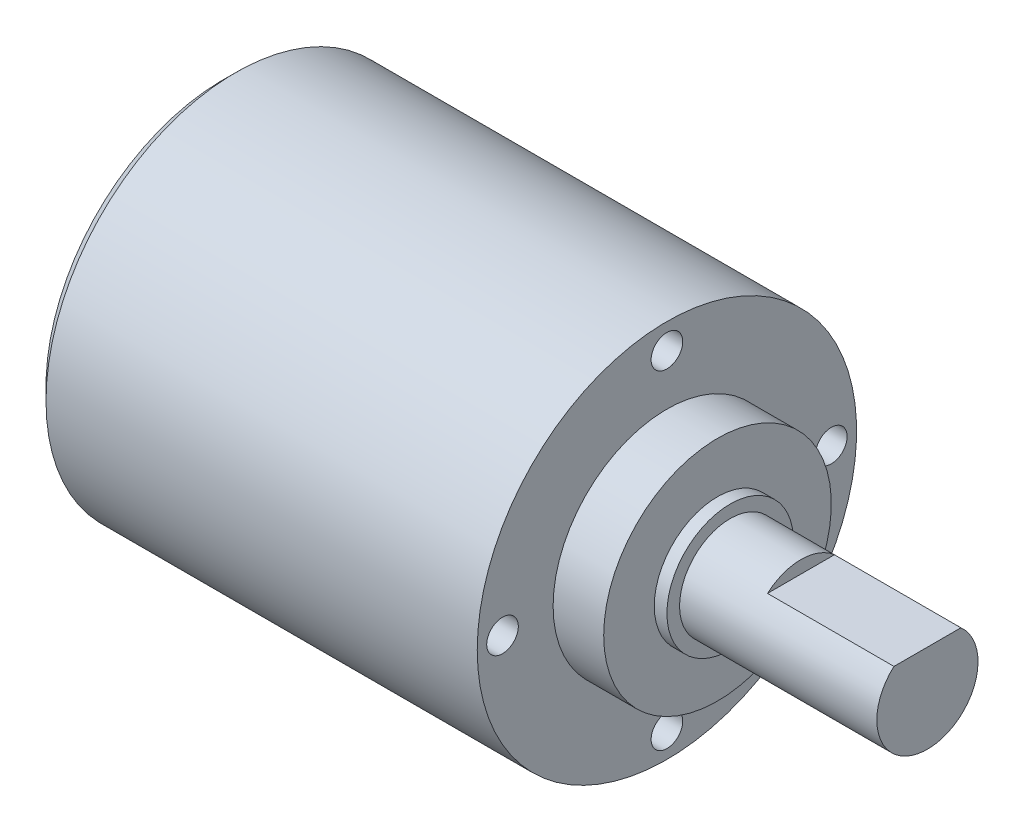
SolidWorks part; units mm, degrees
ref_plane "Plan de face" through (0, 0, 0) normal (0, 0, 1) x (1, 0, 0)
ref_plane "Plan de dessus" through (0, 0, 0) normal (0, 1, 0) x (1, 0, 0)
ref_plane "Plan de droite" through (0, 0, 0) normal (1, 0, 0) x (0, 0, -1)
sketch "Esquisse1" plane through (0, 0, 0) normal (0, 0, 1) x (1, 0, 0)
  line L0 (-27.85, 0) -> (27.85, 0) construction
  line L1 (27.85, 0) -> (27.85, 4)
  line L2 (27.85, 4) -> (12.25, 4)
  line L3 (12.25, 4) -> (12.25, 5)
  line L4 (12.25, 5) -> (11.25, 5)
  line L5 (11.25, 5) -> (11.25, 9)
  line L6 (11.25, 9) -> (7.25, 9)
  line L7 (7.25, 9) -> (7.25, 15)
  line L8 (7.25, 15) -> (-27.85, 15)
  line L9 (-27.85, 15) -> (-27.85, 0)
  line L10 (-27.85, 0) -> (27.85, 0)
  dimension "D1" = 20.6
  dimension "D2" = 4
  dimension "D3" = 1
  dimension "D4" = 8
  dimension "D5" = 10
  dimension "D6" = 18
  dimension "D7" = 30
  dimension "D8" = 35.1
revolve "Révolution1" add sketch "Esquisse1" angle 360 about L0
sketch "Esquisse2" plane through (27.85, 0, 0) normal (1, 0, 0) x (0, 0, -1)
  line L0 (2.6458, 3) -> (-2.6458, 3)
  circle A0 centre (0, 0) radius 4 construction
  arc A1 (2.6458, 3) -> (-2.6458, 3) centre (0, 0) ccw
  dimension "D1" = 3
extrude "Extrusion1" cut sketch "Esquisse2" against normal blind 10
hole_wizard "Trou taraudé M31" positions "Esquisse3D1" profile "Esquisse3" tap size "M3" standard "ISO"
sketch3d "Esquisse3D1"
  line L0 (7.25, 13, 0) -> (7.25, 0, 0) construction
  point P0 (7.25, 13, 0)
  dimension "D1" = 13
sketch "Esquisse3" plane through (7.25, 13, 0) normal (0, 1, 0) x (0, 0, -1)
  line L0 (0, 0) -> (0, 6.2511)
  line L1 (0, 6.2511) -> (1.25, 5.5)
  line L2 (1.25, 5.5) -> (1.25, 0)
  line L5 (1.25, 0) -> (0, 0)
  line L10 (0, 6.2511) -> (-1.25, 5.5) construction
  line L11 (0, -6.35) -> (0, 107.95) construction
  dimension "Diamètre du trou pour taraudage" = 2.5
  dimension "Profondeur du trou pour taraudage" = 5.5
  dimension "Angle de pointe" = 118
cosmetic thread "Filetage de perçage1" parameters "D1"=4, "D2"=3
pattern_circular "Répétition circulaire1" count 4 every 90 about axis through (0, 0, 0) along (1, 0, 0) of "Trou taraudé M31"
chamfer "Chanfrein1" distance 1 angle 45 1 edges at (-27.85, 0, 15)
